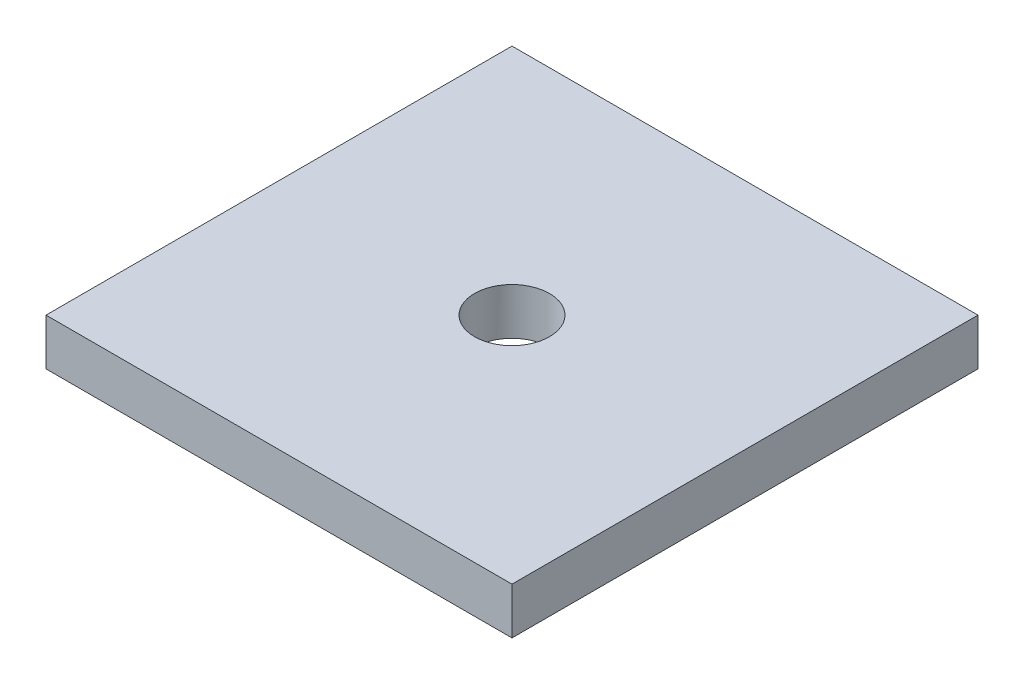
SolidWorks part; units mm, degrees
material "6061-T6 (SS)"
ref_plane "Front" through (0, 0, 0) normal (0, 0, 1) x (1, 0, 0)
ref_plane "Top" through (0, 0, 0) normal (0, 1, 0) x (1, 0, 0)
ref_plane "Right" through (0, 0, 0) normal (1, 0, 0) x (0, 0, -1)
sketch "Sketch1" plane through (0, 0, 0) normal (0, 1, 0) x (1, 0, 0)
  line L1 (0, 0) -> (31.75, 0)
  line L2 (0, 0) -> (0, 31.75)
  line L3 (0, 31.75) -> (31.75, 31.75)
  line L4 (31.75, 0) -> (31.75, 31.75)
  dimension "D1" = 31.75
extrude "Boss-Extrude1" add sketch "Sketch1" along normal blind 3.175
sketch "Sketch4" plane through (0, 3.175, 0) normal (0, 1, 0) x (1, 0, 0)
  line L0 (0, 31.75) -> (31.75, 0) construction
  point P0 (15.875, 15.875)
hole_wizard "1/4-20 Tapped Hole1" positions "Sketch4" profile "Sketch3" tap size "1/4-20" standard "ANSI Inch"
sketch "Sketch3" plane through (15.875, 3.175, -15.875) normal (1, 0, 0) x (0, 0, 1)
  line L0 (0, 0) -> (0, 18.0438)
  line L1 (0, 18.0438) -> (2.5527, 16.51)
  line L2 (2.5527, 16.51) -> (2.5527, 0)
  line L5 (2.5527, 0) -> (0, 0)
  line L10 (0, 18.0438) -> (-2.5527, 16.51) construction
  line L11 (0, -6.35) -> (0, 107.95) construction
  dimension "Tap Drill Dia." = 5.1054
  dimension "Tap Drill Depth" = 16.51
  dimension "Drill Angle" = 118
cosmetic thread "Hole Thread1" parameters "D1"=12.7, "D2"=6.35
